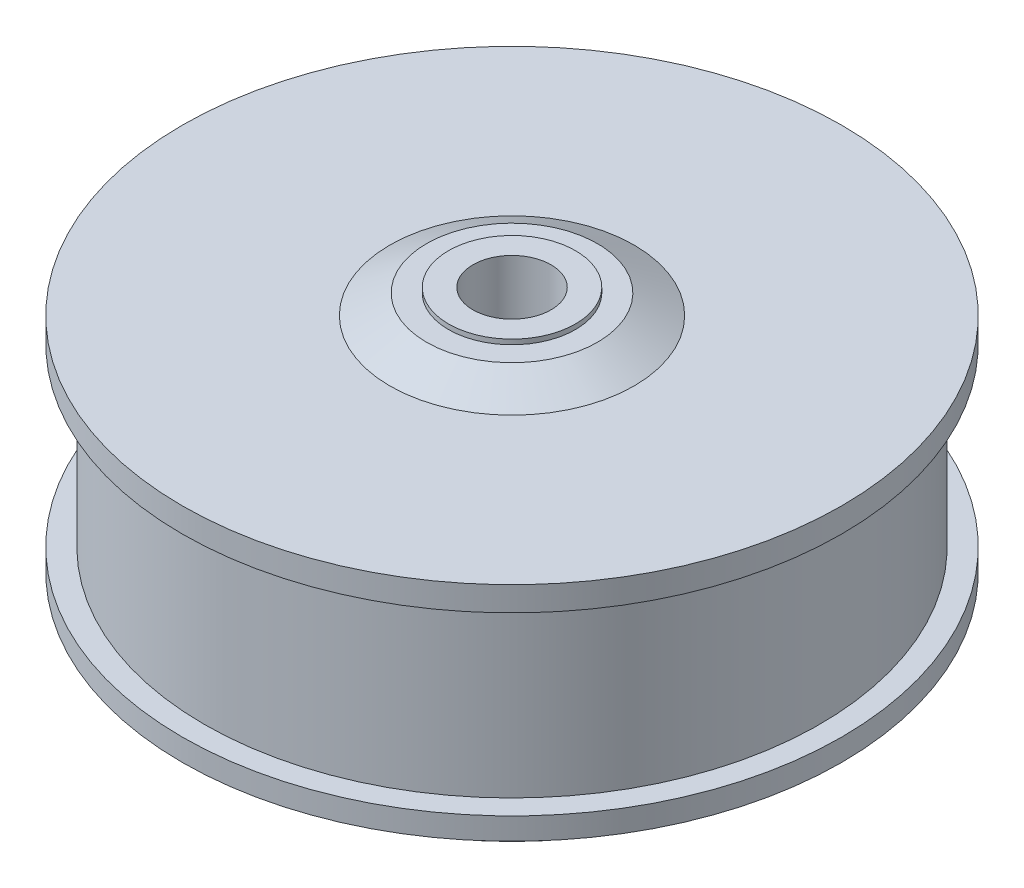
SolidWorks part; units mm, degrees
ref_plane "Front Plane" through (0, 0, 0) normal (0, 0, 1) x (1, 0, 0)
ref_plane "Top Plane" through (0, 0, 0) normal (0, 1, 0) x (1, 0, 0)
ref_plane "Right Plane" through (0, 0, 0) normal (1, 0, 0) x (0, 0, -1)
sketch "Sketch1" plane through (0, 0, 0) normal (0, 0, 1) x (1, 0, 0)
  line L0 (17.5, 60.5) -> (13, 60.5)
  line L1 (17.5, 60.5) -> (25, 56.5)
  line L2 (25, 56.5) -> (67.5, 56.5)
  line L3 (67.5, 56.5) -> (67.5, 51.5)
  line L4 (67.5, 51.5) -> (63, 51.5)
  line L5 (63, 51.5) -> (63, 15.5)
  line L6 (63, 15.5) -> (67.5, 15.5)
  line L7 (67.5, 15.5) -> (67.5, 11)
  line L8 (67.5, 11) -> (61.5, 11)
  line L9 (61.5, 11) -> (52, 0)
  line L10 (52, 0) -> (0, 0)
  line L11 (0, 20.5) -> (0, 0)
  line L12 (8, 61.5) -> (8, 20.5)
  line L13 (13, 60.5) -> (13, 61.5)
  line L14 (13, 61.5) -> (8, 61.5)
  line L15 (8, 20.5) -> (0, 20.5)
  dimension "D2" = 13
  dimension "D3" = 17.5
  dimension "D4" = 4
  dimension "D5" = 5
  dimension "D6" = 36
  dimension "D7" = 4.5
  dimension "D8" = 6
  dimension "D9" = 9.5
  dimension "D10" = 11
  dimension "D11" = 1
  dimension "D12" = 25
  dimension "D13" = 4.5
  dimension "D14" = 67.5
  dimension "D15" = 8
  dimension "D16" = 40
revolve "Revolve1" add sketch "Sketch1" angle 360 about L11
sketch "Sketch2" plane through (0, 0, 0) normal (0, -1, 0) x (1, 0, 0)
  circle A0 centre (0, 27.5) radius 2
  circle A1 centre (19.4454, 19.4454) radius 2
  circle A2 centre (27.5, 0) radius 2
  circle A3 centre (19.4454, -19.4454) radius 2
  circle A4 centre (0, -27.5) radius 2
  circle A5 centre (-19.4454, -19.4454) radius 2
  circle A6 centre (-27.5, 0) radius 2
  circle A7 centre (-19.4454, 19.4454) radius 2
  point P20 (0, 0)
  dimension "D2" = 4
  dimension "D1" = 27.5
  dimension "D3" = 8
extrude "Cut-Extrude1" cut sketch "Sketch2" against normal blind 10
